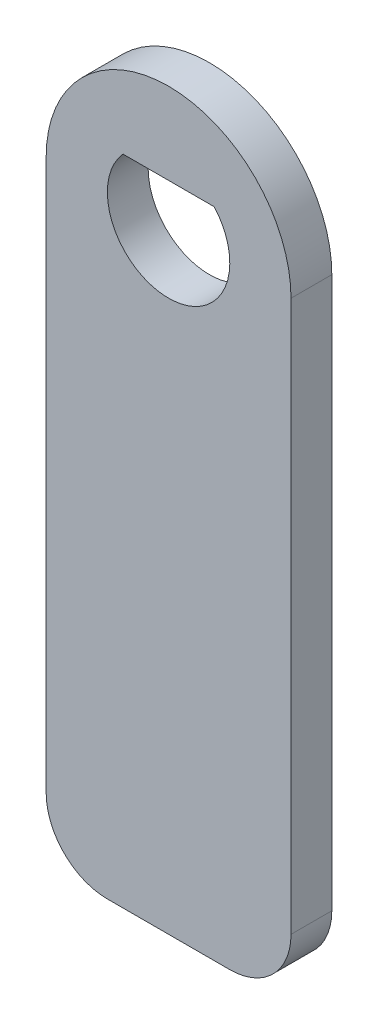
SolidWorks part; units mm, degrees
ref_plane "Front Plane" through (0, 0, 0) normal (0, 0, 1) x (1, 0, 0)
ref_plane "Top Plane" through (0, 0, 0) normal (0, 1, 0) x (1, 0, 0)
ref_plane "Right Plane" through (0, 0, 0) normal (1, 0, 0) x (0, 0, -1)
sketch "Sketch1" plane through (0, 0, 0) normal (0, 0, 1) x (1, 0, 0)
  line L0 (-2.2361, 2) -> (2.2361, 2)
  line L1 (-6, 0) -> (-6, -27)
  line L2 (-3, -30) -> (3, -30)
  line L3 (6, -27) -> (6, 0)
  arc A0 (-2.2361, 2) -> (2.2361, 2) centre (0, 0) ccw
  arc A1 (6, 0) -> (-6, 0) centre (0, 0) ccw
  arc A2 (6, -27) -> (3, -30) centre (3, -27) cw
  arc A3 (-3, -30) -> (-6, -27) centre (-3, -27) cw
  point P10 (6, -30)
  dimension "D1" = 6
  dimension "D3" = 12
  dimension "D5" = 3
  dimension "D6" = 3
  dimension "D2" = 2
  dimension "D4" = 30
extrude "Boss-Extrude1" add sketch "Sketch1" along normal blind 2
